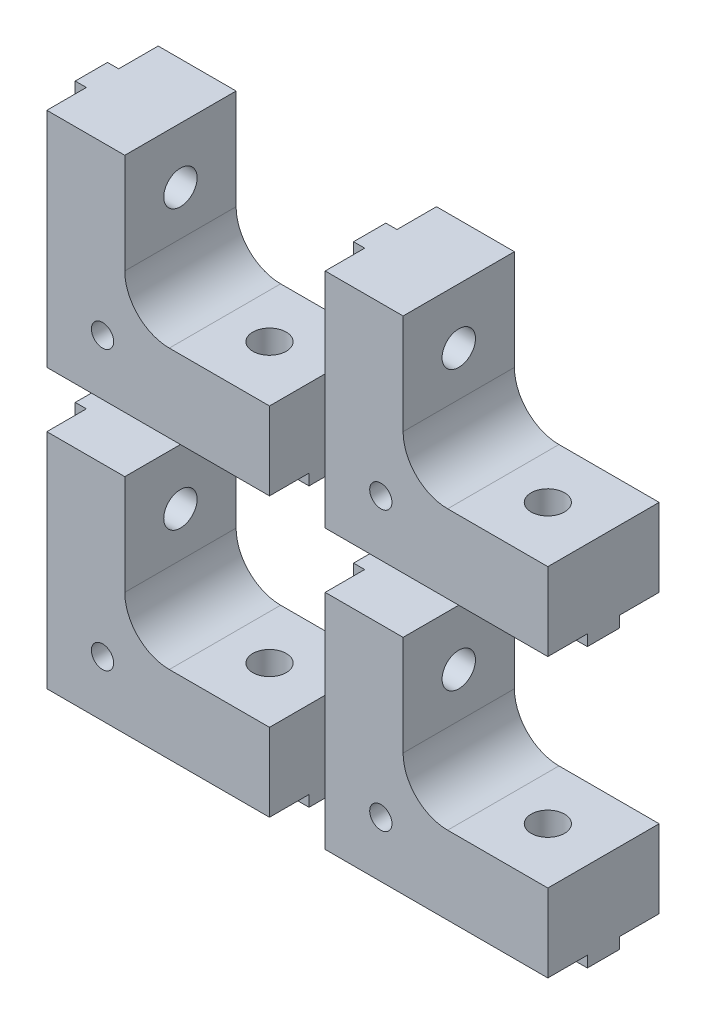
SolidWorks part; units mm, degrees
ref_plane "Front Plane" through (0, 0, 0) normal (0, 0, 1) x (1, 0, 0)
ref_plane "Top Plane" through (0, 0, 0) normal (0, 1, 0) x (1, 0, 0)
ref_plane "Right Plane" through (0, 0, 0) normal (1, 0, 0) x (0, 0, -1)
sketch "Esquisse1" plane through (0, 0, 0) normal (0, 0, 1) x (1, 0, 0)
  line L0 (0, 0) -> (20, 0)
  line L1 (20, 0) -> (20, 7)
  line L2 (20, 7) -> (11, 7)
  line L4 (7, 11) -> (7, 20)
  line L5 (7, 20) -> (0, 20)
  line L6 (0, 20) -> (0, 0)
  arc A0 (11, 7) -> (7, 11) centre (11, 11) cw
  dimension "D1" = 4
  dimension "D2" = 20
  dimension "D3" = 7
extrude "Main" add sketch "Esquisse1" along normal blind 10
sketch "Esquisse4" plane through (0, 0, 0) normal (-1, 0, 0) x (0, 0, 1)
  line L0 (10, 20) -> (0, 20) construction
  line L1 (3.55, 20) -> (6.45, 20)
  line L2 (3.55, 20) -> (3.55, 0)
  line L3 (3.55, 0) -> (6.45, 0)
  line L4 (6.45, 20) -> (6.45, 0)
  line L5 (10, 0) -> (0, 0) construction
  point P8 (5, 20)
  point P9 (5, 20)
  dimension "D1" = 2.9
extrude "MakerBeamFixVertical" add sketch "Esquisse4" along normal blind 1
sketch "Esquisse2" plane through (0, 0, 0) normal (-1, 0, 0) x (0, 0, 1)
  line L0 (10, 20) -> (6.45, 20) construction
  line L1 (10, 20) -> (0, 20) construction
  circle A0 centre (5, 15) radius 1.5
  point P9 (5, 20)
  dimension "D1" = 3
  dimension "D2" = 5
extrude "MakerBeamVerticalHole" cut sketch "Esquisse2" against normal through all both and the other way through all
sketch "Esquisse5" plane through (0, 0, 0) normal (0, -1, 0) x (-1, 0, 0)
  line L0 (-20, -10) -> (-20, 0) construction
  line L1 (0, -3.55) -> (-20, -3.55)
  line L2 (0, -3.55) -> (0, -6.45)
  line L3 (0, -6.45) -> (-20, -6.45)
  line L4 (-20, -3.55) -> (-20, -6.45)
  line L5 (1, -6.45) -> (0, -6.45) construction
extrude "MakerBeamFixHorizontal" add sketch "Esquisse5" along normal blind 1
sketch "Esquisse3" plane through (0, 0, 0) normal (0, -1, 0) x (1, 0, 0)
  line L0 (20, 10) -> (20, 6.45) construction
  line L1 (20, 10) -> (11, 10) construction
  circle A0 centre (15, 5) radius 1.5
  dimension "D1" = 5
  dimension "D2" = 5
  dimension "D3" = 3
extrude "MakerBeamHorizontalHole" cut sketch "Esquisse3" against normal through all both and the other way through all
sketch "Sketch1" plane through (0, 0, 10) normal (0, 0, 1) x (1, 0, 0)
  line L0 (0, 0) -> (20, 0) construction
  line L3 (0, 20) -> (0, 0) construction
  circle A0 centre (5, 5) radius 1
  dimension "D1" = 2
  dimension "D2" = 5
  dimension "D3" = 5
extrude "Cut-Extrude1" cut sketch "Sketch1" against normal through all
pattern_linear "LPattern1" count 2 spacing 25 along (0, 1, 0) count 2 spacing 25 along (1, 0, 0) of bodies 110
